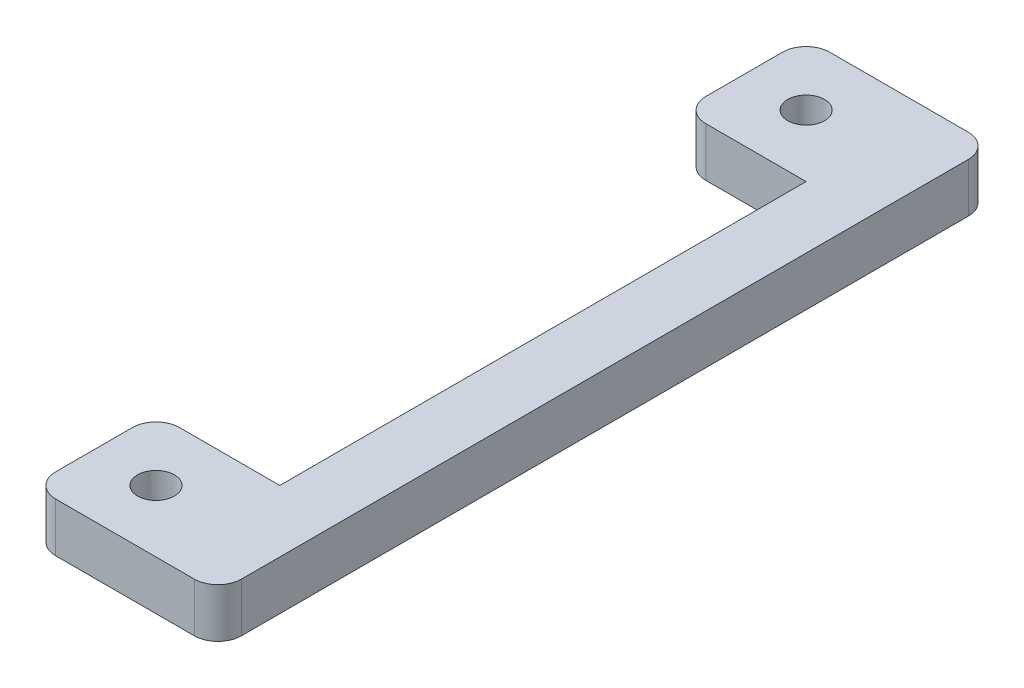
SolidWorks part; units mm, degrees
ref_plane "Front" through (0, 0, 0) normal (0, 0, 1) x (1, 0, 0)
ref_plane "Top" through (0, 0, 0) normal (0, 1, 0) x (1, 0, 0)
ref_plane "Right" through (0, 0, 0) normal (1, 0, 0) x (0, 0, -1)
sketch "Sketch1" plane through (0, 0, 0) normal (0, 1, 0) x (1, 0, 0)
  line L0 (0, 12.5) -> (4, 12.5) construction
  line L1 (0, 25) -> (4, 25)
  line L2 (0, 25) -> (0, 0) construction
  line L3 (2, 2) -> (2, 23) construction
  line L4 (0, 0) -> (4, 0)
  line L5 (4, 25) -> (4, 0) construction
  line L6 (0, 25) -> (0, 21)
  line L7 (0, 21) -> (4, 21)
  line L8 (4, 21) -> (4, 4)
  line L9 (4, 4) -> (0, 4)
  line L10 (0, 4) -> (0, 0)
  line L11 (4, 25) -> (6, 25)
  line L12 (6, 25) -> (6, 0)
  line L13 (6, 0) -> (4, 0)
  circle A5 centre (2, 23) radius 0.5956
  circle A7 centre (2, 2) radius 0.5956
  point P1 (0, 0)
  point P10 (2, 12.5)
  point P22 (8.1726, 0)
  dimension "D5" = 1.1913
  dimension "D1" = 21
  dimension "D2" = 25
  dimension "D3" = 4
  dimension "D4" = 2
extrude "Boss-Extrude1" add sketch "Sketch1" along normal blind 1.5875
fillet "Fillet1" radius 0.762 6 edges at (0, 0.7937, -25) (0, 0.7937, -4) (0, 0.7937, -21) (0, 0.7937, 0) (6, 0.7937, -25) (6, 0.7937, 0)
